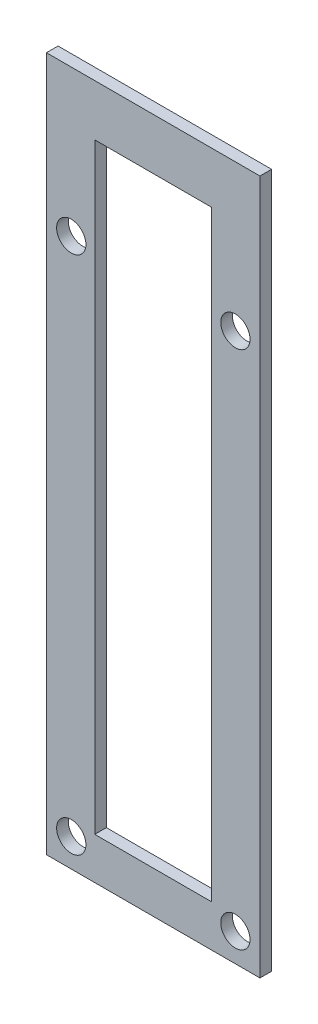
SolidWorks part; units mm, degrees
ref_plane "Front Plane" through (0, 0, 0) normal (0, 0, 1) x (1, 0, 0)
ref_plane "Top Plane" through (0, 0, 0) normal (0, 1, 0) x (1, 0, 0)
ref_plane "Right Plane" through (0, 0, 0) normal (1, 0, 0) x (0, 0, -1)
sketch "Sketch2" plane through (0, 0, 0) normal (0, 0, 1) x (1, 0, 0)
  line L0 (0, 0) -> (0, 94.86)
  line L1 (0, 94.86) -> (-6.6, 94.86)
  line L2 (-6.6, 94.86) -> (-6.6, 5.71)
  line L3 (-6.6, 5.71) -> (-22.56, 5.71)
  line L4 (-22.56, 5.71) -> (-22.56, 94.86)
  line L5 (-22.56, 94.86) -> (-29.16, 94.86)
  line L6 (-29.16, 94.86) -> (-29.16, 0)
  line L7 (-29.16, 0) -> (0, 0)
extrude "Boss-Extrude1" add sketch "Sketch2" along normal blind 1.5875
sketch "Sketch3" plane through (-22.56, 0, 0) normal (1, 0, 0) x (0, 0, -1)
  line L0 (0, 5.71) -> (0, 94.86) construction
  line L1 (-1.5875, 94.86) -> (0, 94.86)
  line L2 (-1.5875, 94.86) -> (-1.5875, 87.8561)
  line L3 (-1.5875, 87.8561) -> (0, 87.8561)
  line L4 (0, 94.86) -> (0, 87.8561)
extrude "Boss-Extrude2" add sketch "Sketch3" along normal up to next
sketch "Sketch4" plane through (0, 0, 1.5875) normal (0, 0, 1) x (1, 0, 0)
  line L0 (0, 94.86) -> (-29.16, 94.86) construction
  circle A0 centre (-3.3544, 47.4281) radius 2
  circle A1 centre (-25.771, 47.4281) radius 2
  circle A2 centre (-25.771, 3.86) radius 2
  circle A3 centre (-3.3544, 3.86) radius 2
  circle A4 centre (-25.771, 74.86) radius 2
  circle A5 centre (-3.3544, 74.86) radius 2
  dimension "D1" = 20
  dimension "D2" = 20
  dimension "D3" = 91
  dimension "D4" = 91
extrude "Cut-Extrude1" cut sketch "Sketch4" against normal blind 15
sketch "Sketch5" plane through (0, 0, 1.5875) normal (0, 0, 1) x (1, 0, 0)
  circle A0 centre (-25.771, 47.4281) radius 2
  circle A1 centre (-3.3544, 47.4281) radius 2
extrude "Boss-Extrude3" add sketch "Sketch5" against normal blind 1.5875
